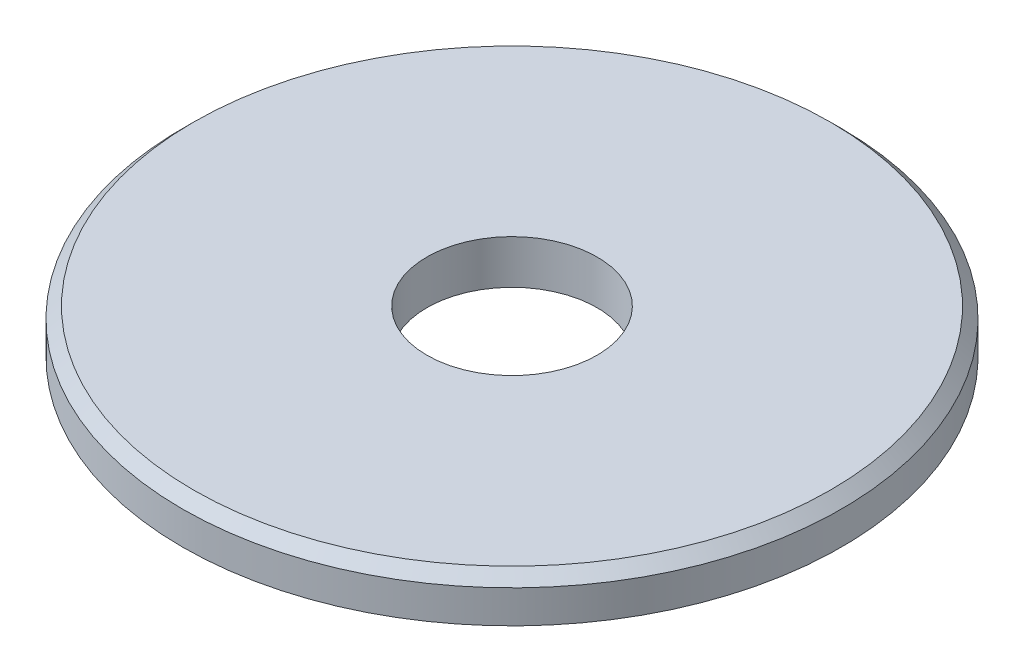
SolidWorks part; units mm, degrees
ref_plane "前视基准面" through (0, 0, 0) normal (0, 0, 1) x (1, 0, 0)
ref_plane "上视基准面" through (0, 0, 0) normal (0, 1, 0) x (1, 0, 0)
ref_plane "右视基准面" through (0, 0, 0) normal (1, 0, 0) x (0, 0, -1)
sketch "草图1" plane through (0, 0, 0) normal (0, 1, 0) x (1, 0, 0)
  circle A0 centre (0, 0) radius 6
  circle A1 centre (0, 0) radius 1.55
  dimension "D1" = 12
  dimension "D2" = 3.1
extrude "凸台-拉伸1" add sketch "草图1" along normal blind 0.8
chamfer "倒角1" distance 0.2 angle 45 1 edges at (0, 0.8, 6)
